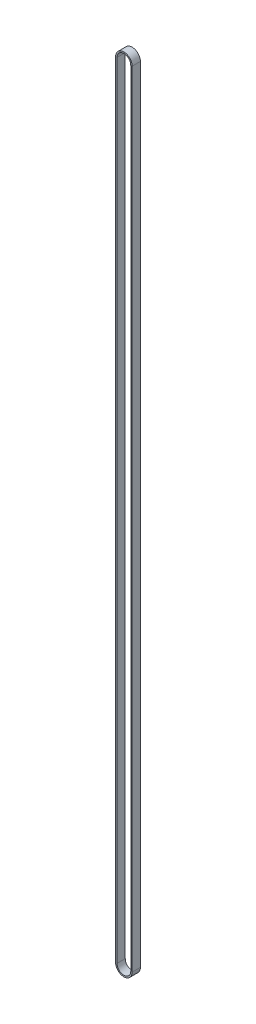
SolidWorks part; units mm, degrees
ref_plane "Front Plane" through (0, 0, 0) normal (0, 0, 1) x (1, 0, 0)
ref_plane "Top Plane" through (0, 0, 0) normal (0, 1, 0) x (1, 0, 0)
ref_plane "Right Plane" through (0, 0, 0) normal (1, 0, 0) x (0, 0, -1)
sketch "Sketch1" plane through (0, 0, 0) normal (0, 0, 1) x (1, 0, 0)
  line L0 (-6, 570) -> (-6, 0)
  line L1 (-5, 570) -> (-5, 0)
  line L2 (6, 0) -> (6, 570)
  line L3 (5, 0) -> (5, 570)
  arc A0 (-6, 0) -> (6, 0) centre (0, 0) ccw
  arc A1 (6, 570) -> (-6, 570) centre (0, 570) ccw
  arc A2 (-5, 0) -> (5, 0) centre (0, 0) ccw
  arc A3 (5, 570) -> (-5, 570) centre (0, 570) ccw
  dimension "D1" = 12
  dimension "D2" = 12
  dimension "D3" = 570
  dimension "D4" = 1
extrude "Boss-Extrude1" add sketch "Sketch1" along normal blind 6
